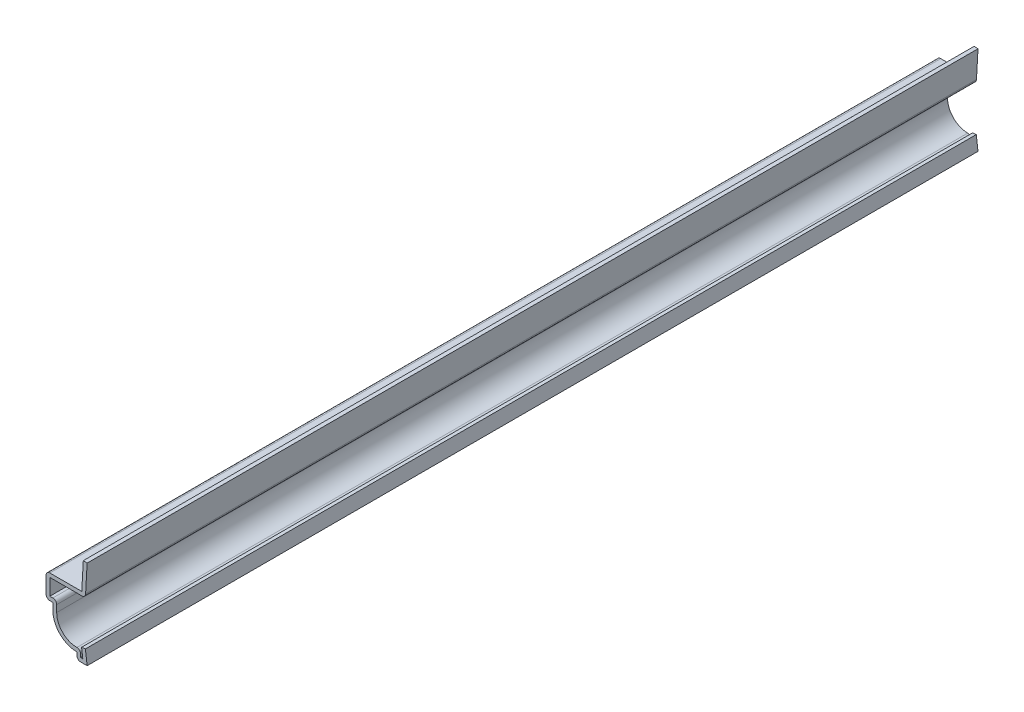
SolidWorks part; units mm, degrees
ref_plane "Front Plane" through (0, 0, 0) normal (0, 0, 1) x (1, 0, 0)
ref_plane "Top Plane" through (0, 0, 0) normal (0, 1, 0) x (1, 0, 0)
ref_plane "Right Plane" through (0, 0, 0) normal (1, 0, 0) x (0, 0, -1)
sketch "Sketch1" plane through (0, 0, 0) normal (0, 0, 1) x (1, 0, 0)
  line L0 (-0.3969, 3.175) -> (0, 0)
  line L1 (0, 0) -> (-2.3813, 0)
  line L2 (-2.3813, 0) -> (-2.3812, 1.5875)
  line L3 (-7.9375, 7.1437) -> (-7.9375, 8.7312)
  line L4 (-7.9375, 8.7312) -> (-9.525, 8.7312)
  line L5 (-9.525, 8.7312) -> (-9.525, 14.2875)
  line L6 (-9.525, 14.2875) -> (-1.2382, 14.2875)
  line L7 (-1.2382, 14.2875) -> (-0.8876, 20.6375)
  line L8 (-1.279, 3.0647) -> (-1.007, 0.889)
  line L9 (-1.007, 0.889) -> (-1.4923, 0.889)
  line L10 (-1.4923, 0.889) -> (-1.4923, 2.5619)
  line L11 (-7.0485, 7.1438) -> (-7.0485, 9.6203)
  line L12 (-7.0485, 9.6203) -> (-8.636, 9.6203)
  line L13 (-8.636, 9.6203) -> (-8.636, 13.3985)
  line L14 (-8.636, 13.3985) -> (-0.3969, 13.3985)
  line L15 (-0.3969, 13.3985) -> (0, 20.5885)
  line L16 (-0.3969, 3.175) -> (-1.279, 3.0647)
  line L17 (-0.8876, 20.6375) -> (0, 20.5885)
  arc A0 (-2.3812, 1.5875) -> (-7.9375, 7.1437) centre (-2.3813, 7.1437) cw
  arc A1 (-1.4923, 2.5619) -> (-7.0485, 7.1438) centre (-2.3813, 7.1437) cw
  point P23 (0, 0)
  dimension "D5" = 5.5562
  dimension "D1" = 14.2875
  dimension "D2" = 6.35
  dimension "D3" = 5.5562
  dimension "D4" = 7.1437
  dimension "D6" = 9.525
  dimension "D7" = 2.3813
  dimension "D8" = 3.175
  dimension "D9" = 0.3969
  dimension "D11" = 0.3969
  dimension "D10" = 0.889
extrude "Boss-Extrude1" add sketch "Sketch1" against normal blind 206.375
fillet "Fillet1" radius 0.889 6 edges at (-1.4922, 2.5619, -103.1875) (-2.3813, 0, -103.1875) (-7.0485, 9.6203, -103.1875) (-9.525, 8.7312, -103.1875) (-9.525, 14.2875, -103.1875) (-0.3969, 13.3985, -103.1875)
